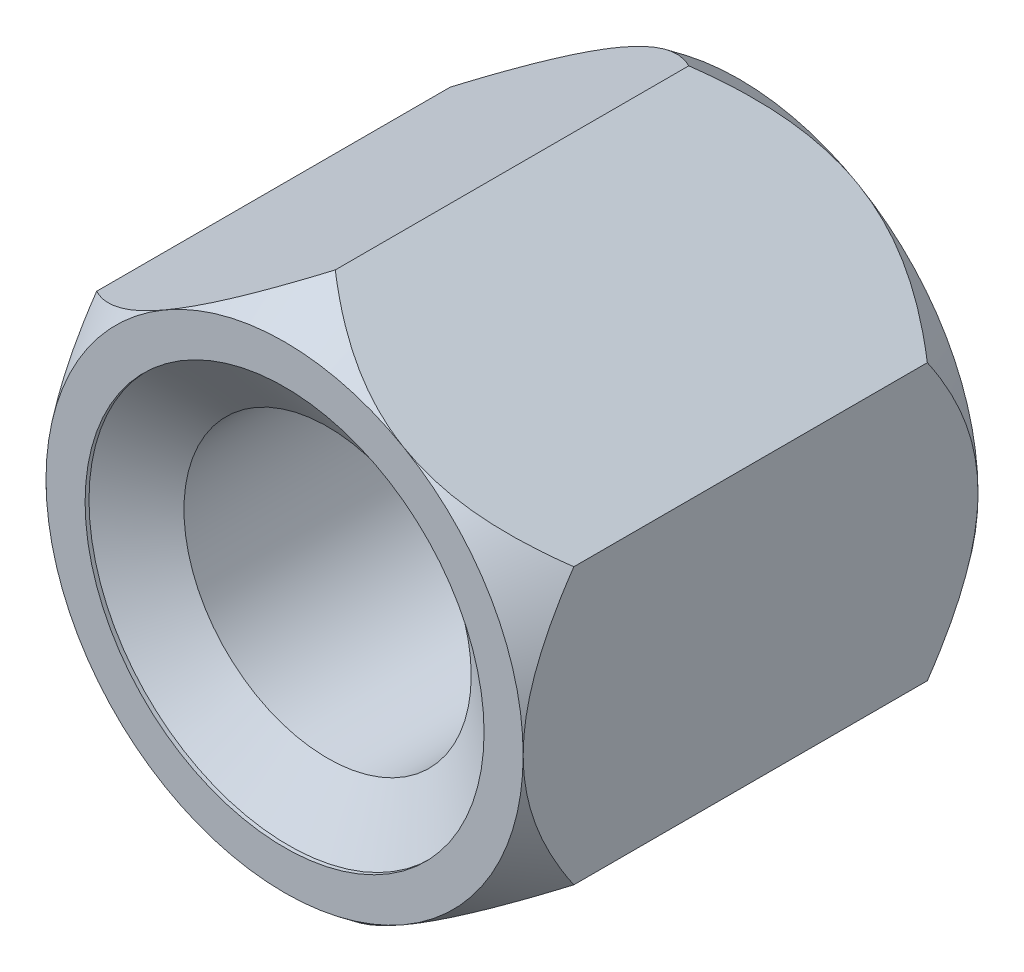
SolidWorks part; units mm, degrees
extrude "BaseNut" add sketch "BaseNutSke" against normal blind 5.7
sketch "BaseNutSke" plane through (0, 0, 0) normal (0, 0, 1) x (1, 0, 0)
  line L6 (2.99, 1.7263) -> (2.99, -1.7263)
  line L7 (-2.99, 1.7263) -> (-2.99, -1.7263)
  line L8 (2.99, 1.7263) -> (0, 3.4526)
  line L9 (0, 3.4526) -> (-2.99, 1.7263)
  line L10 (-2.99, -1.7263) -> (0, -3.4526)
  line L11 (0, -3.4526) -> (2.99, -1.7263)
  circle A0 centre (0, 0) radius 1.8
  dimension "Tap_drill" = 3.6
  dimension "Width_flats" = 5.98
  dimension "D2" = 2.99
  dimension "D3" = 2.99
  dimension "D1" = 120
  dimension "D4" = 2.99
pattern_linear "ThdSchPat" [suppressed]
revolve "ThreadSchematic" [suppressed] cut sketch "ThdSchSke" angle 360 about L6
sketch "ThdSchSke" plane through (0, 0, 0) normal (0, 1, 0) x (1, 0, 0)
  line L0 (-3.175, 0.0254) -> (-1.8, 0.9882)
  line L1 (-1.8, 0.9882) -> (-0.9, 0.9882)
  line L2 (-0.9, 0.9882) -> (-0.9, -0.9374)
  line L3 (-0.9, -0.9374) -> (-1.8, -0.9374)
  line L4 (-1.8, -0.9374) -> (-3.175, 0.0254)
  line L5 (-3.175, 1.27) -> (3.175, 1.27) construction
  line L6 (0, 1.27) -> (0, -2.9874) construction
  line L7 (0, 5.1601) -> (0, 0.5389) construction
  dimension "SideAngle" = 55
  dimension "Advance" = 1.27
  dimension "D1" = 0.0254
ref_plane "Plane1" through (0, 0, 0) normal (0, 0, 1) x (1, 0, 0)
ref_plane "Plane2" through (0, 0, 0) normal (0, 1, 0) x (1, 0, 0)
ref_plane "Plane3" through (0, 0, 0) normal (1, 0, 0) x (0, 0, -1)
sketch "Sketch4" plane through (0, 0, 0) normal (1, 0, 0) x (0, 0, -1)
  line L0 (5.7, 2.99) -> (5.2936, 2.99)
  line L1 (5.7, 2.99) -> (5.7, 16.1526)
  line L2 (5.2936, 16.1526) -> (5.7, 16.1526)
  line L3 (5.2936, 16.1526) -> (5.2936, 2.99)
  line L4 (0, 0) -> (34.925, 0) construction
  line L6 (5.7, 1.7263) -> (5.7, 3.4526) construction
  line L7 (0, 2.99) -> (-12.7, 2.99)
  line L8 (0, 1.7263) -> (0, 3.4526) construction
  line L9 (0.635, 3.4526) -> (0.635, 16.1526)
  line L10 (0.635, 16.1526) -> (-12.7, 16.1526)
  line L11 (-12.7, 16.1526) -> (-12.7, 2.99)
  line L12 (0, 2.99) -> (0.635, 3.4526)
  line L14 (0, 1.7263) -> (0, -1.7263) construction
  line L15 (5.7, 3.4526) -> (0, 3.4526) construction
  dimension "D1" = 2.99
  dimension "D2" = 0.635
  dimension "D3" = 12.7
  dimension "D4" = 12.7
revolve "Bearing-Face" [suppressed] cut sketch "Sketch4" angle 360 about L4
sketch "Sketch3" plane through (0, 0, 0) normal (1, 0, 0) x (0, 0, -1)
  line L0 (5.7, 2.99) -> (5.065, 3.4526)
  line L1 (5.065, 3.4526) -> (5.065, 16.1526)
  line L2 (5.065, 16.1526) -> (18.4, 16.1526)
  line L3 (18.4, 16.1526) -> (18.4, 2.99)
  line L4 (18.4, 2.99) -> (5.7, 2.99)
  line L5 (5.7, 1.7263) -> (5.7, 3.4526) construction
  line L6 (5.7, 3.4526) -> (0, 3.4526) construction
  line L7 (0, 0) -> (38.6776, 0) construction
  line L8 (5.7, 0) -> (0, 0) construction
  line L9 (2.85, 3.4526) -> (2.85, 44.222) construction
  line L10 (0.635, 16.1526) -> (-12.7, 16.1526)
  line L11 (-12.7, 16.1526) -> (-12.7, 2.99)
  line L12 (-12.7, 2.99) -> (0, 2.99)
  line L13 (0, 2.99) -> (0.635, 3.4526)
  line L14 (0.635, 3.4526) -> (0.635, 16.1526)
  line L16 (5.7, 3.4526) -> (0, 3.4526) construction
  dimension "D1" = 2.99
  dimension "D2" = 0.635
  dimension "D4" = 12.7
  dimension "D3" = 12.7
revolve "Double-Chamfer" cut sketch "Sketch3" angle 360 about L7
sketch "Sketch5" plane through (0, 0, 0) normal (1, 0, 0) x (0, 0, -1)
  line L0 (5.6502, 2.5) -> (4.5911, 0.9875)
  line L1 (5.701, 2.5) -> (5.6502, 2.5)
  line L2 (5.701, 2.5) -> (5.701, 0.9875)
  line L3 (5.701, 0.9875) -> (4.5911, 0.9875)
  line L6 (-0.002, 2.5) -> (0.0488, 2.5)
  line L7 (0.0488, 2.5) -> (1.1079, 0.9875)
  line L9 (1.1079, 0.9875) -> (-0.002, 0.9875)
  line L10 (-0.002, 0.9875) -> (-0.002, 2.5)
  line L11 (25.0375, 0) -> (38.388, 0) construction
  line L12 (5.7, 0) -> (0, 0) construction
  dimension "D1" = 35
  dimension "D2" = 0.0508
  dimension "ThreadMajor" = 2.5
  dimension "Offset1" = 5.701
revolve "EndChamfer" cut sketch "Sketch5" angle 360 about L11
equation "\"D2@BaseNutSke\"= \"Width_flats@BaseNutSke\" / 2"
equation "\"D3@BaseNutSke\" = \"Width_flats@BaseNutSke\" / 2"
equation "\"D1@Sketch3\" = \"Width_flats@BaseNutSke\" /2"
equation "\"D1@Sketch4\" = \"D2@BaseNutSke\""
equation "\"D4@BaseNutSke\" = \"D3@BaseNutSke\""
equation "\"Tap_Drill@ThdSchSke\" = \"Tap_drill@BaseNutSke\""
equation "\"OverCut@ThdSchSke\" = \"Tap_Drill@ThdSchSke\" * 0.5"
equation "\"Num_threads@ThdSchPat\" = int(  ( \"Thickness@BaseNut\" - 0.002 ) / \"Advance@ThdSchSke\" + 0.999 )  + 1"
equation "\"Advance@ThdSchPat\" = ( \"Thickness@BaseNut\" - 0.002 ) /  (\"Num_threads@ThdSchPat\" - 1) 'relax it"
equation "' \"Num_threads@ThdSchPat\" = \"Num_threads@ThdSchPat\" - sgn( \"Num_threads@ThdSchPat\" - 1) '---chamfered tips only---"
equation "\"Offset1@Sketch5\" = \"Thickness@BaseNut\" + 0.001"
equation "\"Offset2@Sketch5\" = \"Offset1@Sketch5\" + 0.002"
